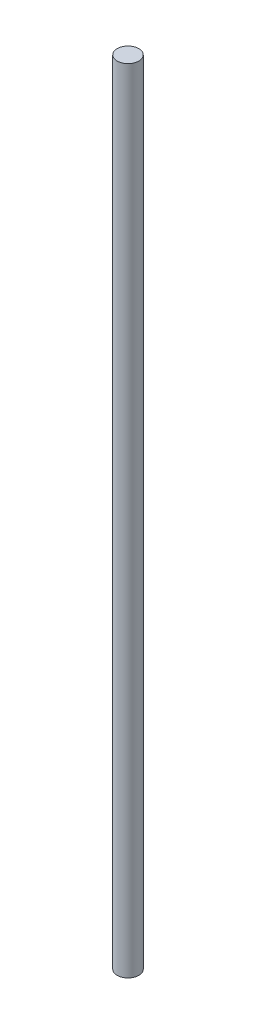
SolidWorks part; units mm, degrees
ref_plane "Front Plane" through (0, 0, 0) normal (0, 0, 1) x (1, 0, 0)
ref_plane "Top Plane" through (0, 0, 0) normal (0, 1, 0) x (1, 0, 0)
ref_plane "Right Plane" through (0, 0, 0) normal (1, 0, 0) x (0, 0, -1)
sketch "Sketch1" plane through (0, 0, 0) normal (0, 1, 0) x (1, 0, 0)
  circle A0 centre (0, 0) radius 4.7625
  dimension "D1" = 9.525
extrude "Boss-Extrude1" add sketch "Sketch1" along normal blind 349.25
equation "\"Lead_Screw_Diam\" = 0.375in"
equation "\"Mid_Coupler_Length\" = 12in"
equation "\"Lead_Screw_Length\" = \"Mid_Coupler_Length\" + 2*0.375in + 2*0.5in"
equation "\"D1@Sketch1\"=\"Lead_Screw_Diam\""
equation "\"D1@Boss-Extrude1\"=\"Lead_Screw_Length\""
